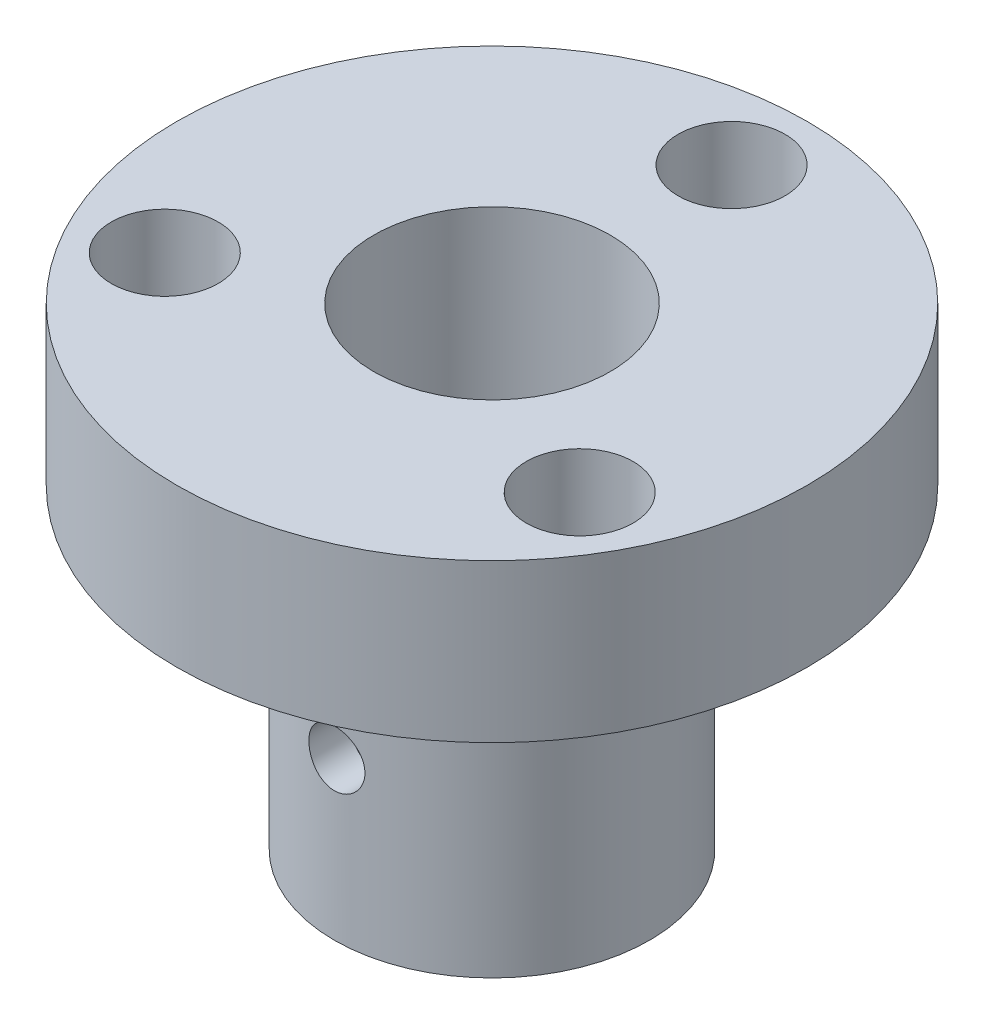
SolidWorks part; units mm, degrees
ref_plane "Front Plane" through (0, 0, 0) normal (0, 0, 1) x (1, 0, 0)
ref_plane "Top Plane" through (0, 0, 0) normal (0, 1, 0) x (1, 0, 0)
ref_plane "Right Plane" through (0, 0, 0) normal (1, 0, 0) x (0, 0, -1)
sketch "Sketch1" plane through (0, 0, 0) normal (0, 1, 0) x (1, 0, 0)
  circle A0 centre (0, 0) radius 6.35
  dimension "D1" = 12.7
extrude "Boss-Extrude1" add sketch "Sketch1" along normal blind 12.7
sketch "Sketch2" plane through (0, 12.7, 0) normal (0, 1, 0) x (1, 0, 0)
  circle A0 centre (0, 0) radius 12.7
  dimension "D1" = 25.4
extrude "Boss-Extrude2" add sketch "Sketch2" along normal blind 6.35
sketch "Sketch3" plane through (0, 19.05, 0) normal (0, 1, 0) x (1, 0, 0)
  line L0 (0, 0) -> (0, 12.7) construction
  line L1 (0, 0) -> (12.7, 0) construction
  circle A0 centre (0, 0) radius 4.7676
  circle A1 centre (0, 0) radius 12.7 construction
  dimension "D1" = 9.5352
extrude "Cut-Extrude1" cut sketch "Sketch3" against normal through all
hole_wizard "#18 (0.1695) Diameter Hole1" positions "Sketch5" profile "Sketch6" hole size "#18" standard "ANSI Inch"
sketch "Sketch5" plane through (0, 19.05, 0) normal (0, 1, 0) x (1, 0, 0)
  line L0 (0, 0) -> (0, 12.7) construction
  line L4 (0, 0) -> (-10.9985, -6.35) construction
  line L5 (0, 0) -> (10.9985, -6.35) construction
  circle A0 centre (0, 0) radius 12.7 construction
  point P17 (0, 9.652)
  point P50 (-8.3589, -4.826)
  point P52 (8.3589, -4.826)
  dimension "D1" = 9.652
  dimension "D2" = 120
  dimension "D3" = 120
  dimension "D4" = 9.652
  dimension "D5" = 9.652
sketch "Sketch6" plane through (0, 19.05, -9.652) normal (1, 0, 0) x (0, 0, 1)
  line L0 (0, 0) -> (0, 26.6934)
  line L1 (0, 26.6934) -> (2.1526, 25.4)
  line L2 (2.1526, 25.4) -> (2.1526, 0)
  line L5 (2.1526, 0) -> (0, 0)
  line L10 (0, 26.6934) -> (-2.1527, 25.4) construction
  line L11 (0, -6.35) -> (0, 107.95) construction
  dimension "Hole Dia." = 4.3053
  dimension "Hole Depth" = 25.4
  dimension "Drill Angle" = 118
hole_wizard "#43 (0.089) Diameter Hole1" positions "Sketch9" profile "Sketch8" hole size "#43" standard "ANSI Inch"
sketch "Sketch9" plane through (0, 0, 0) normal (0, 0, 1) x (1, 0, 0)
  line L0 (0, 0) -> (0, 20.0457) construction
  point P12 (0, 6.35)
  dimension "D1" = 6.35
sketch "Sketch8" plane through (0, 6.35, 0) normal (1, 0, 0) x (0, 1, 0)
  line L0 (0, 0) -> (0, 26.0792)
  line L1 (0, 26.0792) -> (1.1303, 25.4)
  line L2 (1.1303, 25.4) -> (1.1303, 0)
  line L5 (1.1303, 0) -> (0, 0)
  line L10 (0, 26.0792) -> (-1.1303, 25.4) construction
  line L11 (0, -6.35) -> (0, 107.95) construction
  dimension "Hole Dia." = 2.2606
  dimension "Hole Depth" = 25.4
  dimension "Drill Angle" = 118
